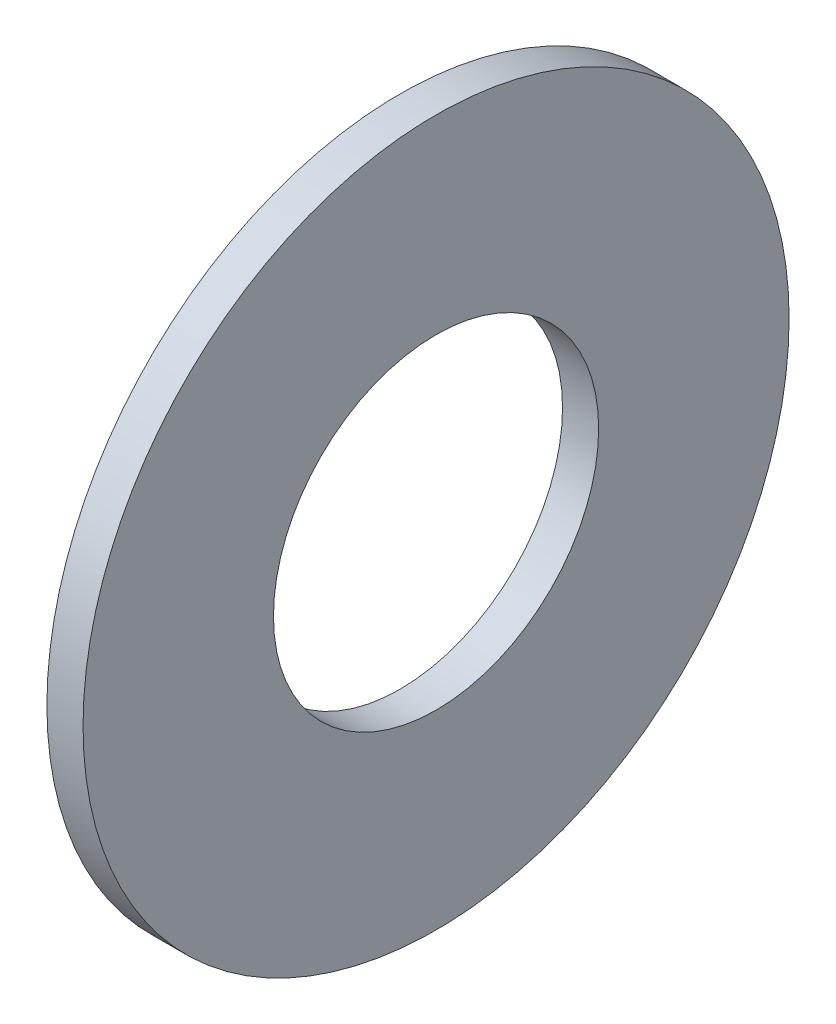
SolidWorks part; units mm, degrees
material "Magnesium Alloy"
ref_plane "Front Plane" through (0, 0, 0) normal (0, 0, 1) x (1, 0, 0)
ref_plane "Top Plane" through (0, 0, 0) normal (0, 1, 0) x (1, 0, 0)
ref_plane "Right Plane" through (0, 0, 0) normal (1, 0, 0) x (0, 0, -1)
sketch "Sketch1" plane through (0, 0, 0) normal (1, 0, 0) x (0, 0, -1)
  circle A0 centre (0, 0) radius 4.885
  circle A1 centre (0, 0) radius 2.25
  dimension "D1" = 9.77
  dimension "D2" = 4.5
extrude "Boss-Extrude1" add sketch "Sketch1" along normal blind 0.5
